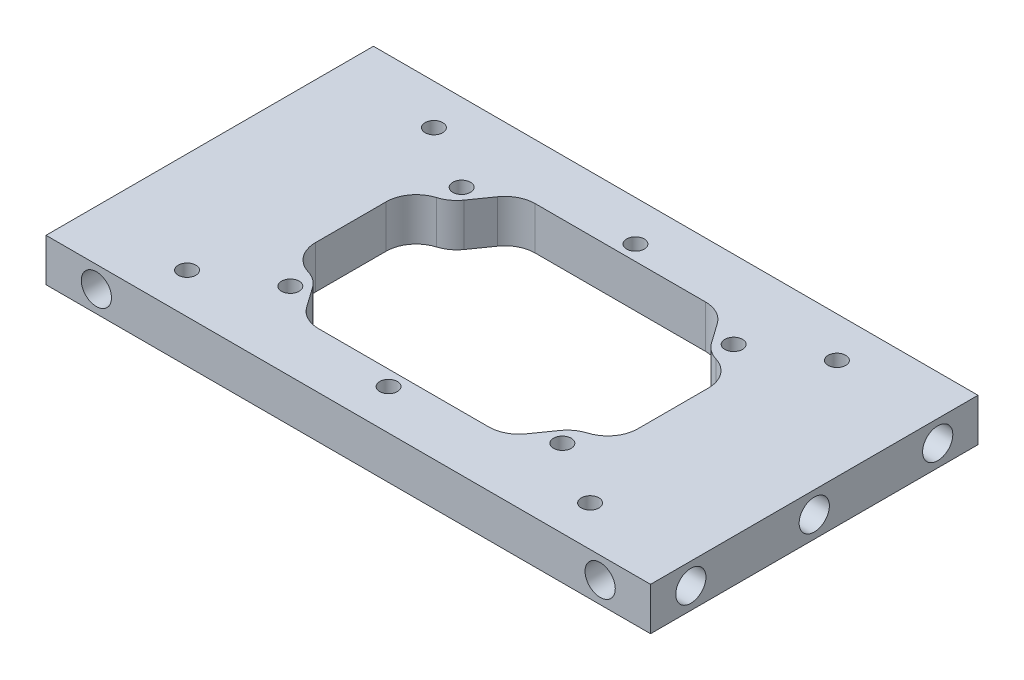
SolidWorks part; units mm, degrees
ref_plane "Front Plane" through (0, 0, 0) normal (0, 0, 1) x (1, 0, 0)
ref_plane "Top Plane" through (0, 0, 0) normal (0, 1, 0) x (1, 0, 0)
ref_plane "Right Plane" through (0, 0, 0) normal (1, 0, 0) x (0, 0, -1)
sketch "Sketch1" plane through (0, 0, 0) normal (1, 0, 0) x (0, 0, -1)
  line L1 (-32.5, -4.25) -> (32.5, -4.25)
  line L2 (-32.5, -4.25) -> (-32.5, 4.25)
  line L3 (-32.5, 4.25) -> (32.5, 4.25)
  line L4 (32.5, -4.25) -> (32.5, 4.25)
  line L5 (-32.5, -4.25) -> (32.5, 4.25) construction
  line L6 (-32.5, 4.25) -> (32.5, -4.25) construction
  point P0 (0, 0)
  dimension "D1" = 8.5
  dimension "D2" = 65
extrude "Boss-Extrude1" add sketch "Sketch1" along normal blind 120
hole_wizard "Ø6.0mm Dowel Hole1" positions "Sketch2" profile "Sketch3" hole size "Ø6.0" standard "ANSI Metric"
sketch "Sketch2" plane through (120, 0, 0) normal (1, 0, 0) x (0, 0, -1)
  line L0 (-32.5, 4.25) -> (-32.5, -4.25) construction
  line L1 (32.5, -4.25) -> (32.5, 4.25) construction
  point P0 (-24.5, 0)
  point P2 (0, 0)
  point P5 (24.5, 0)
  dimension "D1" = 8
  dimension "D2" = 8
sketch "Sketch3" plane through (120, 0, 24.5) normal (0, 1, 0) x (0, 0, -1)
  line L0 (0, 0) -> (0, 11.8026)
  line L1 (0, 11.8026) -> (3, 10)
  line L2 (3, 10) -> (3, 0)
  line L5 (3, 0) -> (0, 0)
  line L10 (0, 11.8026) -> (-3, 10) construction
  line L11 (0, -6.35) -> (0, 107.95) construction
  dimension "Hole Dia." = 6
  dimension "Hole Depth" = 10
  dimension "Drill Angle" = 118
ref_plane "Plane1" through (60, 0, 0) normal (1, 0, 0) x (0, 0, -1)
mirror "Mirror1" about plane through (60, 0, 0) normal (1, 0, 0) of "Ø6.0mm Dowel Hole1"
hole_wizard "Ø6.0mm Dowel Hole2" positions "Sketch4" profile "Sketch5" hole size "Ø6.0" standard "ANSI Metric"
sketch "Sketch4" plane through (0, 0, -32.5) normal (0, 0, -1) x (-1, 0, 0)
  line L0 (-120, -4.25) -> (-120, 4.25) construction
  line L1 (0, -4.25) -> (0, 4.25) construction
  line L2 (-120, 0) -> (0, 0) construction
  point P0 (-110, 0)
  point P2 (-10, 0)
  dimension "D1" = 10
  dimension "D2" = 10
sketch "Sketch5" plane through (110, 0, -32.5) normal (1, 0, 0) x (0, 1, 0)
  line L0 (0, 0) -> (0, 9.8026)
  line L1 (0, 9.8026) -> (3, 8)
  line L2 (3, 8) -> (3, 0)
  line L5 (3, 0) -> (0, 0)
  line L10 (0, 9.8026) -> (-3, 8) construction
  line L11 (0, -6.35) -> (0, 107.95) construction
  dimension "Hole Dia." = 6
  dimension "Hole Depth" = 8
  dimension "Drill Angle" = 118
mirror "Mirror2" about plane through (0, 0, 0) normal (0, 0, 1) of "Ø6.0mm Dowel Hole2"
sketch "Sketch6" plane through (0, 4.25, 0) normal (0, 1, 0) x (1, 0, 0)
  line L0 (86, -7) -> (86, 7) construction
  line L1 (80, -7) -> (80, 7)
  line L2 (92, -7) -> (92, 7)
  line L3 (120, 32.5) -> (120, -32.5) construction
  arc A0 (80, -7) -> (92, -7) centre (86, -7) ccw
  arc A1 (92, 7) -> (80, 7) centre (86, 7) ccw
  point P2 (86, 0)
  point P10 (120, 0)
  dimension "D3" = 12
  dimension "D1" = 40
  dimension "D2" = 14
extrude "Cut-Extrude1" cut sketch "Sketch6" against normal through all
mirror "Mirror3" about plane through (60, 0, 0) normal (1, 0, 0) of "Cut-Extrude1"
sketch "Sketch7" plane through (0, 4.25, 0) normal (0, 1, 0) x (1, 0, 0)
  line L0 (120, 32.5) -> (0, 32.5) construction
  line L1 (87, 17) -> (33, 17)
  line L2 (87, 17) -> (87, -17)
  line L3 (87, -17) -> (33, -17)
  line L4 (33, 17) -> (33, -17)
  line L5 (87, 17) -> (33, -17) construction
  line L6 (87, -17) -> (33, 17) construction
  point P0 (60, 0)
  point P8 (60, 32.5)
  dimension "D1" = 54
  dimension "D2" = 34
hole_wizard "Ø3.0mm Dowel Hole1" positions "Sketch8" profile "Sketch9" hole size "Ø3.0" standard "ANSI Metric" end condition through all
sketch "Sketch8" plane through (0, 4.25, 0) normal (0, 1, 0) x (1, 0, 0)
  line L0 (120, -32.5) -> (0, -32.5) construction
  line L1 (120, 32.5) -> (0, 32.5) construction
  line L2 (120, 32.5) -> (120, -32.5) construction
  line L3 (0, 32.5) -> (0, -32.5) construction
  point P0 (87, -17)
  point P3 (87, 17)
  point P6 (33, 17)
  point P9 (33, -17)
  point P13 (100, -24.5)
  point P15 (60, -24.5)
  point P17 (20, -24.5)
  point P19 (100, 24.5)
  point P21 (60, 24.5)
  point P23 (20, 24.5)
  point P40 (60, 32.5)
  dimension "D1" = 8
  dimension "D2" = 8
  dimension "D3" = 20
  dimension "D4" = 20
sketch "Sketch9" plane through (87, 4.25, 17) normal (1, 0, 0) x (0, 0, 1)
  line L0 (0, 0) -> (0, 8.5)
  line L1 (0, 8.5) -> (1.75, 8.5)
  line L2 (1.75, 8.5) -> (1.75, 0)
  line L5 (1.75, 0) -> (0, 0)
  line L11 (0, -6.35) -> (0, 107.95) construction
  dimension "Thru Hole Dia." = 3.5
  dimension "Thru Hole Depth" = 8.5
sketch "Sketch10" plane through (0, -4.25, 0) normal (0, -1, 0) x (1, 0, 0)
  line L0 (120, 32.5) -> (0, 32.5) construction
  line L1 (40, -21.5) -> (80, -21.5)
  line L2 (40, -21.5) -> (40, 21.5)
  line L3 (40, 21.5) -> (80, 21.5)
  line L4 (80, -21.5) -> (80, 21.5)
  line L5 (40, -21.5) -> (80, 21.5) construction
  line L6 (40, 21.5) -> (80, -21.5) construction
  line L7 (0, 32.5) -> (0, -32.5) construction
  line L8 (40, 21.5) -> (34, 13)
  line L9 (34, -13) -> (40, -21.5)
  line L10 (40, -7) -> (40, 7) construction
  line L11 (80, 21.5) -> (86, 13)
  line L12 (86, -13) -> (80, -21.5)
  arc A0 (40, 7) -> (28, 7) centre (34, 7) ccw construction
  arc A1 (28, -7) -> (40, -7) centre (34, -7) ccw construction
  arc A2 (28, -7) -> (40, -7) centre (34, -7) ccw
  arc A3 (40, 7) -> (28, 7) centre (34, 7) ccw
  arc A4 (80, -7) -> (92, -7) centre (86, -7) ccw construction
  arc A5 (92, 7) -> (80, 7) centre (86, 7) ccw construction
  arc A6 (80, -7) -> (92, -7) centre (86, -7) ccw
  arc A7 (92, 7) -> (80, 7) centre (86, 7) ccw
  point P0 (60, 0)
  point P7 (60, 32.5)
  point P11 (0, 0)
  line M17 (80, -7) -> (80, 7)
  arc M18 (80, 7) -> (92, 7) centre (86, 7) cw
  arc M20 (92, -7) -> (80, -7) centre (86, -7) cw
  arc M21 (28, 7) -> (40, 7) centre (34, 7) cw
  line M22 (40, 7) -> (40, -7)
  arc M23 (40, -7) -> (28, -7) centre (34, -7) cw
  dimension "D1" = 43
extrude "Cut-Extrude2" cut sketch "Sketch10" against normal through all contours L2 L8 M21 | L1 L4 L3 L2 M17 M22 | L9 L2 M23 | L11 L4 M18 | L12 L4 M20
fillet "Fillet1" radius 6 8 edges at (34, 0, -13) (40, 0, -21.5) (34, 0, 13) (40, 0, 21.5) (80, 0, -21.5) (86, 0, -13) (80, 0, 21.5) (86, 0, 13)
